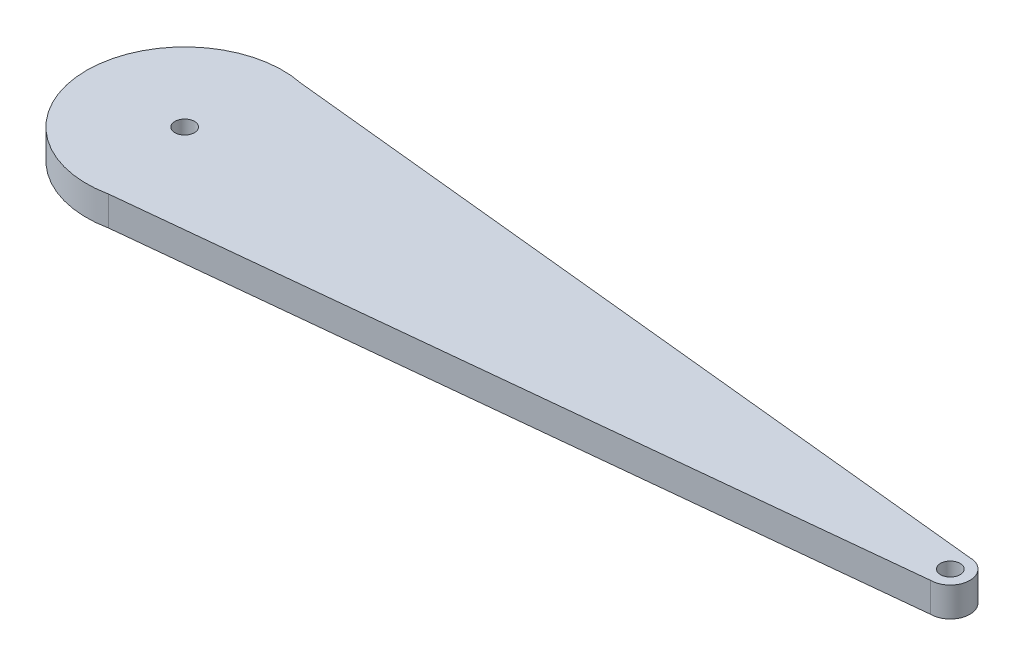
SolidWorks part; units mm, degrees
ref_plane "Front Plane" through (0, 0, 0) normal (0, 0, 1) x (1, 0, 0)
ref_plane "Top Plane" through (0, 0, 0) normal (0, 1, 0) x (1, 0, 0)
ref_plane "Right Plane" through (0, 0, 0) normal (1, 0, 0) x (0, 0, -1)
sketch "Sketch1" plane through (0, 0, 0) normal (0, 1, 0) x (1, 0, 0)
  line L1 (0, 0) -> (90, 0)
  line L2 (0, 0) -> (0, 20)
  line L3 (0, 20) -> (90, 20)
  line L4 (90, 0) -> (90, 20)
  dimension "D1" = 20
  dimension "D2" = 90
extrude "Boss-Extrude1" add sketch "Sketch1" along normal blind 3
sketch "Sketch2" plane through (0, 3, 0) normal (0, 1, 0) x (1, 0, 0)
  line L0 (0, 0) -> (90, 0) construction
  line L1 (0, 20) -> (0, 0) construction
  line L2 (90, 0) -> (90, 20) construction
  line L3 (10, 20) -> (88, 12)
  line L4 (10, 0) -> (88, 8)
  line L9 (0, 0) -> (90, 0)
  line L10 (90, 0) -> (90, 20)
  line L11 (90, 20) -> (0, 20)
  line L12 (0, 20) -> (0, 0)
  line L13 (0, 0) -> (90, 0)
  line L14 (90, 0) -> (90, 20)
  line L15 (90, 20) -> (0, 20)
  line L16 (0, 20) -> (0, 0)
  arc A0 (12.0299, 19.7918) -> (12.0299, 0.2082) centre (10, 10) ccw
  arc A1 (88, 8) -> (88, 12) centre (88, 10) ccw
  line M3 (0, 20) -> (0, 0)
  line M4 (0, 0) -> (90, 0)
  line M5 (90, 0) -> (90, 20)
  line M6 (90, 20) -> (0, 20)
  dimension "D1" = 20
  dimension "D2" = 4
  dimension "D3" = 0
extrude "Cut-Extrude1" cut sketch "Sketch2" against normal through all contours A1 L14 A0 L3 M6 | A1 L4 A0 M4 M5 | A0 L16 M4 | A0 M6 M3
sketch "Sketch3" plane through (0, 3, 0) normal (0, 1, 0) x (1, 0, 0)
  circle A0 centre (10, 10) radius 1
  circle A1 centre (88, 10) radius 1
  point P8 (0, 0)
  dimension "D2" = 2
  dimension "D3" = 2
extrude "Cut-Extrude2" cut sketch "Sketch3" against normal through all
